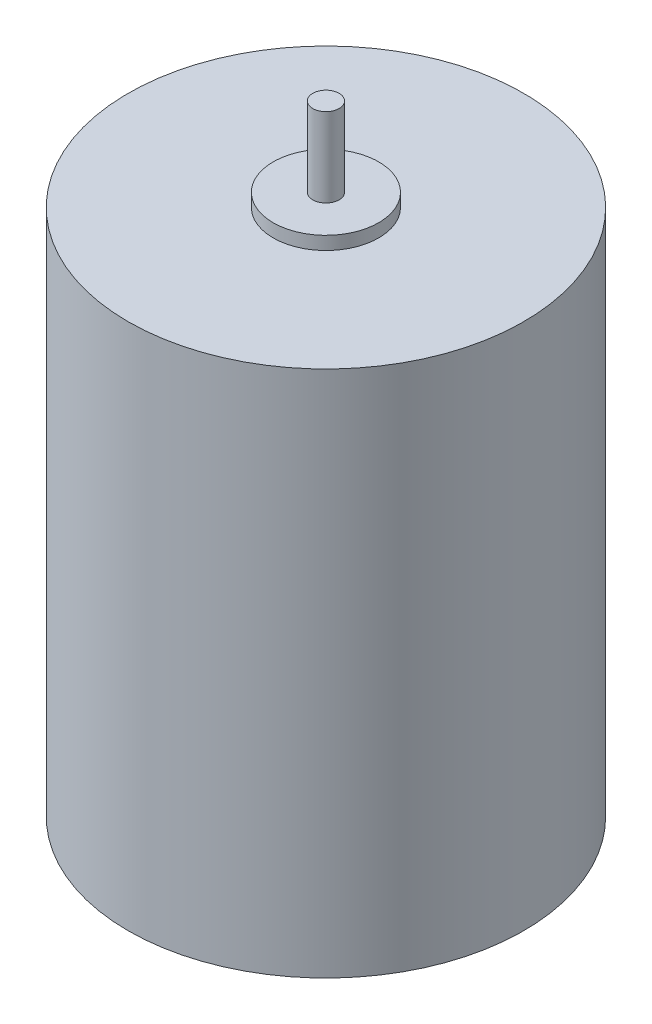
SolidWorks part; units mm, degrees
ref_plane "Face" through (0, 0, 0) normal (0, 0, 1) x (1, 0, 0)
ref_plane "Dessus" through (0, 0, 0) normal (0, 1, 0) x (1, 0, 0)
ref_plane "Droite" through (0, 0, 0) normal (1, 0, 0) x (0, 0, -1)
sketch "Esquisse1" plane through (0, 0, 0) normal (0, 1, 0) x (1, 0, 0)
  circle A0 centre (0, 0) radius 15
  dimension "D1" = 30
extrude "Extrusion1" add sketch "Esquisse1" along normal blind 40
sketch "Esquisse2" plane through (0, 40, 0) normal (0, 1, 0) x (1, 0, 0)
  circle A0 centre (0, 0) radius 4
  circle A1 centre (0, 0) radius 15 construction
  dimension "D1" = 8
extrude "Extrusion2" add sketch "Esquisse2" along normal blind 1
sketch "Esquisse3" plane through (0, 41, 0) normal (0, 1, 0) x (1, 0, 0)
  circle A0 centre (0, 0) radius 1
  circle A1 centre (0, 0) radius 4 construction
  dimension "D1" = 2
extrude "Extrusion3" add sketch "Esquisse3" along normal blind 6
